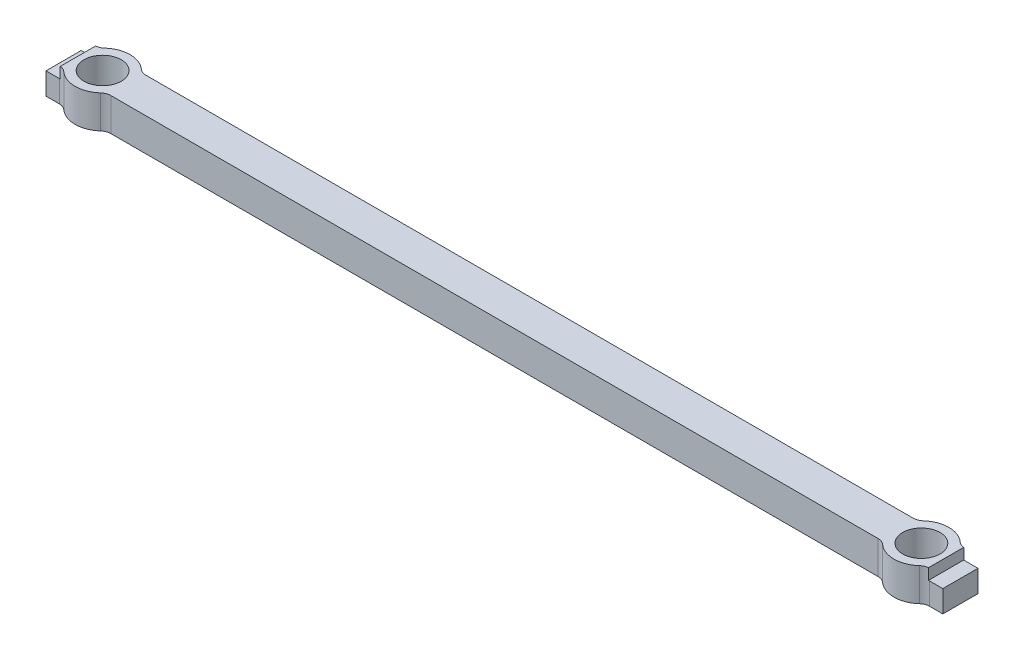
SolidWorks part; units mm, degrees
ref_plane "Front Plane" through (0, 0, 0) normal (0, 0, 1) x (1, 0, 0)
ref_plane "Top Plane" through (0, 0, 0) normal (0, 1, 0) x (1, 0, 0)
ref_plane "Right Plane" through (0, 0, 0) normal (1, 0, 0) x (0, 0, -1)
sketch "Sketch1" plane through (0, 0, 0) normal (0, 1, 0) x (1, 0, 0)
  line L0 (-39.5, 2.5) -> (-39.5, -2.5) construction
  line L1 (-40.8, 2.5) -> (40.8, 2.5)
  line L2 (-40.8, 2.5) -> (-40.8, -2.5)
  line L3 (-40.8, -2.5) -> (40.8, -2.5)
  line L4 (40.8, 2.5) -> (40.8, -2.5)
  line L5 (-40.8, 2.5) -> (40.8, -2.5) construction
  line L6 (-40.8, -2.5) -> (40.8, 2.5) construction
  line L7 (-37.25, 2.5) -> (-37.25, -2.5) construction
  line L8 (-40.8, 0) -> (40.8, 0) construction
  line L9 (0, 2.5) -> (0, -2.5) construction
  line L11 (40.8, 1.6) -> (-40.8, 1.6)
  line L12 (40.8, 1.6) -> (40.8, -1.6)
  line L13 (40.8, -1.6) -> (-40.8, -1.6)
  line L14 (-40.8, 1.6) -> (-40.8, -1.6)
  line L15 (40.8, 1.6) -> (-40.8, -1.6) construction
  line L16 (40.8, -1.6) -> (-40.8, 1.6) construction
  circle A0 centre (-37.25, 0) radius 1.7
  circle A1 centre (-37.25, 0) radius 2.5
  circle A2 centre (37.25, 0) radius 1.7
  circle A3 centre (37.25, 0) radius 2.5
  point P0 (0, 0)
  point P17 (0, 0)
  dimension "D5" = 3.4
  dimension "D1" = 81.6
  dimension "D2" = 5
  dimension "D3" = 1.3
  dimension "D4" = 2.25
  dimension "D6" = 3.2
extrude "Shape" add sketch "Sketch1" along normal blind 3 contours L11 A3 L13 L4 | A3 L11 A2 L13 | A3 L13 | A3 L11 | A3 L13 A2 L11 | L13 A3 L11 A1 | L13 A1 L11 A0 | L11 A1 | L11 A1 L13 A0 | A1 L13 | A1 L11 L2 L13
fillet "Mill fillets" radius 1 8 edges at (35.3291, 1.5, -1.6) (39.1709, 1.5, -1.6) (-39.1709, 1.5, -1.6) (-35.3291, 1.5, -1.6) (-35.3291, 1.5, 1.6) (-39.1709, 1.5, 1.6) (39.1709, 1.5, 1.6) (35.3291, 1.5, 1.6)
sketch "Sketch2" plane through (0, 3, 0) normal (0, 1, 0) x (1, 0, 0)
  line L0 (-39.5, 1.6043) -> (-39.5, -1.6043)
  line L1 (0, 1.6) -> (0, -1.6) construction
  line L2 (39.5, 1.6043) -> (39.5, -1.6043)
  line L8 (34.9069, 1.6) -> (-34.9069, 1.6)
  line L9 (-39.5931, 1.6) -> (-40.8, 1.6)
  line L10 (-40.8, 1.6) -> (-40.8, -1.6)
  line L11 (-40.8, -1.6) -> (-39.5931, -1.6)
  line L12 (-34.9069, -1.6) -> (34.9069, -1.6)
  line L13 (39.5931, -1.6) -> (40.8, -1.6)
  line L14 (40.8, -1.6) -> (40.8, 1.6)
  line L15 (40.8, 1.6) -> (39.5931, 1.6)
  line L16 (34.9069, 1.6) -> (-34.9069, 1.6)
  line L17 (-39.5931, 1.6) -> (-40.8, 1.6)
  line L18 (-40.8, 1.6) -> (-40.8, -1.6)
  line L19 (-40.8, -1.6) -> (-39.5931, -1.6)
  line L20 (-34.9069, -1.6) -> (34.9069, -1.6)
  line L21 (39.5931, -1.6) -> (40.8, -1.6)
  line L22 (40.8, -1.6) -> (40.8, 1.6)
  line L23 (40.8, 1.6) -> (39.5931, 1.6)
  arc A12 (-35.5764, 1.8571) -> (-34.9069, 1.6) centre (-34.9069, 2.6) ccw
  arc A13 (-35.5764, 1.8571) -> (-38.9236, 1.8571) centre (-37.25, 0) ccw
  arc A14 (-39.5931, 1.6) -> (-38.9236, 1.8571) centre (-39.5931, 2.6) ccw
  arc A15 (-38.9236, -1.8571) -> (-39.5931, -1.6) centre (-39.5931, -2.6) ccw
  arc A16 (-38.9236, -1.8571) -> (-35.5764, -1.8571) centre (-37.25, 0) ccw
  arc A17 (-34.9069, -1.6) -> (-35.5764, -1.8571) centre (-34.9069, -2.6) ccw
  arc A18 (35.5764, -1.8571) -> (34.9069, -1.6) centre (34.9069, -2.6) ccw
  arc A19 (35.5764, -1.8571) -> (38.9236, -1.8571) centre (37.25, 0) ccw
  arc A20 (39.5931, -1.6) -> (38.9236, -1.8571) centre (39.5931, -2.6) ccw
  arc A21 (38.9236, 1.8571) -> (39.5931, 1.6) centre (39.5931, 2.6) ccw
  arc A22 (38.9236, 1.8571) -> (35.5764, 1.8571) centre (37.25, 0) ccw
  arc A23 (34.9069, 1.6) -> (35.5764, 1.8571) centre (34.9069, 2.6) ccw
  arc A24 (-35.5764, 1.8571) -> (-34.9069, 1.6) centre (-34.9069, 2.6) ccw
  arc A25 (-35.5764, 1.8571) -> (-38.9236, 1.8571) centre (-37.25, 0) ccw
  arc A26 (-39.5931, 1.6) -> (-38.9236, 1.8571) centre (-39.5931, 2.6) ccw
  arc A27 (-38.9236, -1.8571) -> (-39.5931, -1.6) centre (-39.5931, -2.6) ccw
  arc A28 (-38.9236, -1.8571) -> (-35.5764, -1.8571) centre (-37.25, 0) ccw
  arc A29 (-34.9069, -1.6) -> (-35.5764, -1.8571) centre (-34.9069, -2.6) ccw
  arc A30 (35.5764, -1.8571) -> (34.9069, -1.6) centre (34.9069, -2.6) ccw
  arc A31 (35.5764, -1.8571) -> (38.9236, -1.8571) centre (37.25, 0) ccw
  arc A32 (39.5931, -1.6) -> (38.9236, -1.8571) centre (39.5931, -2.6) ccw
  arc A33 (38.9236, 1.8571) -> (39.5931, 1.6) centre (39.5931, 2.6) ccw
  arc A34 (38.9236, 1.8571) -> (35.5764, 1.8571) centre (37.25, 0) ccw
  arc A35 (34.9069, 1.6) -> (35.5764, 1.8571) centre (34.9069, 2.6) ccw
  arc M26 (-38.9236, 1.8571) -> (-39.5931, 1.6) centre (-39.5931, 2.6) cw
  line M27 (-39.5931, 1.6) -> (-40.8, 1.6)
  line M28 (-40.8, 1.6) -> (-40.8, -1.6)
  line M29 (-40.8, -1.6) -> (-39.5931, -1.6)
  arc M30 (-39.5931, -1.6) -> (-38.9236, -1.8571) centre (-39.5931, -2.6) cw
  arc M36 (38.9236, -1.8571) -> (39.5931, -1.6) centre (39.5931, -2.6) cw
  line M37 (39.5931, -1.6) -> (40.8, -1.6)
  line M38 (40.8, -1.6) -> (40.8, 1.6)
  line M39 (40.8, 1.6) -> (39.5931, 1.6)
  arc M40 (39.5931, 1.6) -> (38.9236, 1.8571) centre (39.5931, 2.6) cw
  dimension "D2" = 1.3
  dimension "D1" = 0
extrude "Edge cuts" cut sketch "Sketch2" against normal offset from surface (1 mm away) 2 contours L0 M26 M27 M28 M29 M30 | L2 M40 M36 M37 M38 M39 | L18 L19 A27 A28 A29 L20 A30 A31 A32 L21 L22 L23 A33 A34 A35 L16 A24 A25 A26 L17
sketch "Coordinate system sketch" plane through (0, 3, 0) normal (0, 1, 0) x (1, 0, 0)
  line L0 (37.25, -2.5) -> (40.8, -2.5) construction
  line L1 (40.8, -2.5) -> (40.8, -1.6) construction
  arc A0 (35.5764, -1.8571) -> (38.9236, -1.8571) centre (37.25, 0) ccw construction
  point P5 (0, 0)
  point P8 (40.788, -1.9748)
  point P9 (0, 0)
sketch "Edge milling sketch" plane through (0, 2, 0) normal (0, 1, 0) x (1, 0, 0)
  line L0 (-41.9584, 0) -> (5.4055, 0) construction
  line L1 (-40.5, 1.6043) -> (-40.5, -1.6043) construction
  line L2 (-39.5, 1.6043) -> (-39.5, -1.6043)
  line L3 (-41.5, 1.6043) -> (-41.5, -1.6043)
  line L4 (0, 6.8742) -> (0, -9.8727) construction
  line L5 (40.5, 1.6043) -> (40.5, -1.6043) construction
  line L6 (39.5, 1.6043) -> (39.5, -1.6043)
  line L7 (41.5, 1.6043) -> (41.5, -1.6043)
  arc A0 (-39.5, 1.6043) -> (-41.5, 1.6043) centre (-40.5, 1.6043) ccw
  arc A1 (-41.5, -1.6043) -> (-39.5, -1.6043) centre (-40.5, -1.6043) ccw
  arc A2 (39.5, 1.6043) -> (41.5, 1.6043) centre (40.5, 1.6043) cw
  arc A3 (41.5, -1.6043) -> (39.5, -1.6043) centre (40.5, -1.6043) cw
  point P5 (-40.5, 0)
  point P15 (40.5, 0)
  point P20 (-39.865, 1.4872)
  point P22 (-39.7406, 1.3379)
  dimension "D1" = 2
